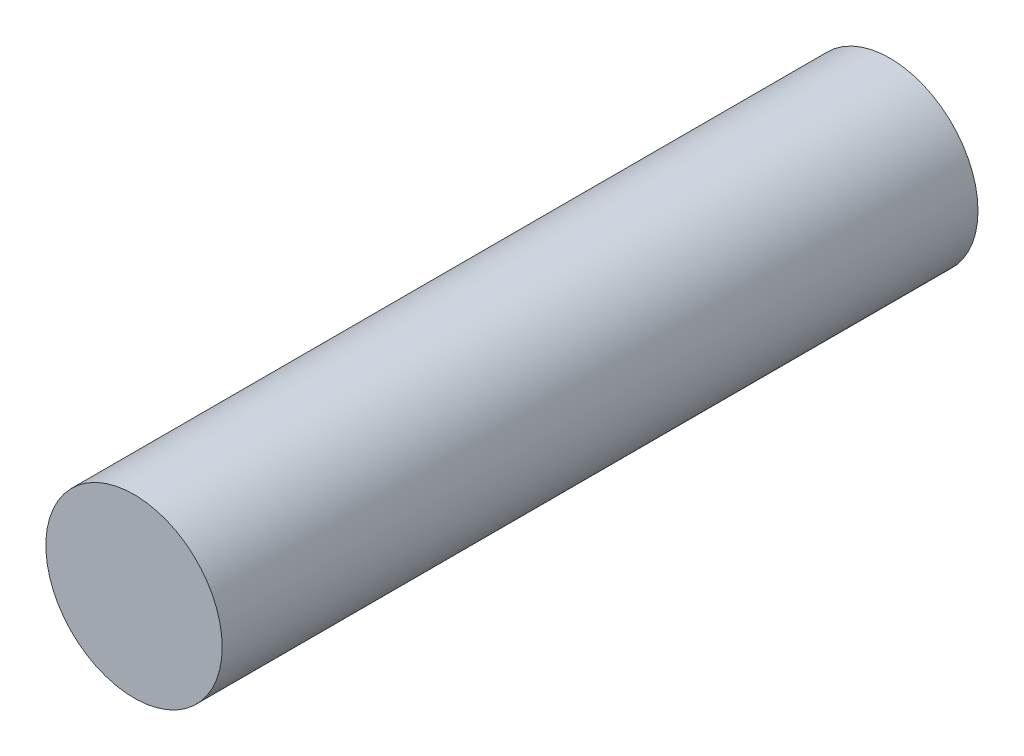
SolidWorks part; units mm, degrees
ref_plane "Front Plane" through (0, 0, 0) normal (0, 0, 1) x (1, 0, 0)
ref_plane "Top Plane" through (0, 0, 0) normal (0, 1, 0) x (1, 0, 0)
ref_plane "Right Plane" through (0, 0, 0) normal (1, 0, 0) x (0, 0, -1)
sketch "Sketch1" plane through (0, 0, 0) normal (0, 0, 1) x (1, 0, 0)
  circle A0 centre (0, 0) radius 3.5
  dimension "D1" = 7
extrude "Boss-Extrude1" add sketch "Sketch1" along normal blind 30
